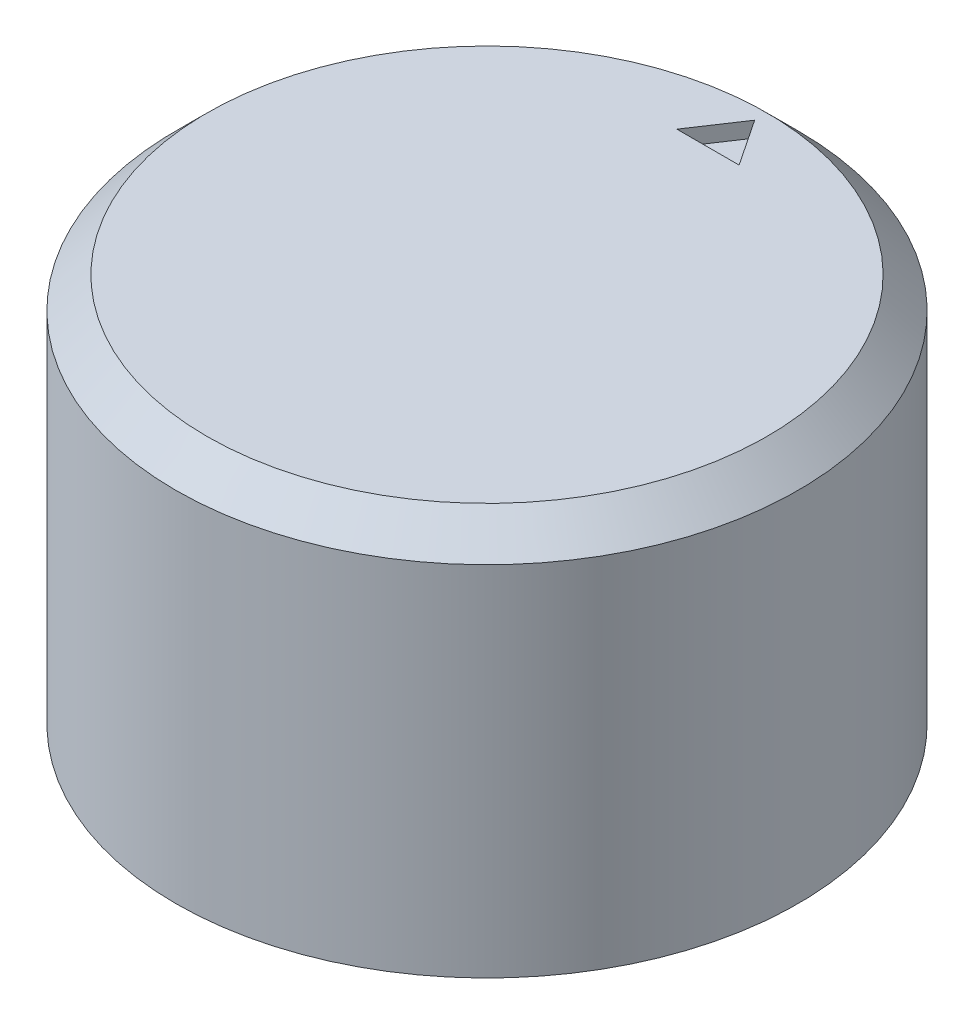
SolidWorks part; units mm, degrees
ref_plane "Front Plane" through (0, 0, 0) normal (0, 0, 1) x (1, 0, 0)
ref_plane "Top Plane" through (0, 0, 0) normal (0, 1, 0) x (1, 0, 0)
ref_plane "Right Plane" through (0, 0, 0) normal (1, 0, 0) x (0, 0, -1)
sketch "Sketch1" plane through (0, 0, 0) normal (0, 1, 0) x (1, 0, 0)
  circle A0 centre (0, 0) radius 10
  dimension "D1" = 20
extrude "Boss-Extrude1" add sketch "Sketch1" along normal blind 12.5
sketch "Sketch2" plane through (0, 0, 0) normal (0, -1, 0) x (1, 0, 0)
  line L0 (-2.5981, 1.5) -> (2.5981, 1.5)
  arc A0 (-2.5981, 1.5) -> (2.5981, 1.5) centre (0, 0) ccw
  dimension "D1" = 6
  dimension "D2" = 1.5
extrude "Cut-Extrude1" cut sketch "Sketch2" against normal blind 10
sketch "Sketch3" plane through (0, 12.5, 0) normal (0, 1, 0) x (1, 0, 0)
  line L0 (-1, 7.1) -> (0, 8.6)
  line L1 (0, 8.6) -> (1, 7.1)
  line L2 (1, 7.1) -> (-1, 7.1)
  point P2 (0, 7.1)
  dimension "D1" = 2
  dimension "D2" = 1.5
  dimension "D3" = 7.1
extrude "Cut-Extrude2" cut sketch "Sketch3" against normal blind 0.5
chamfer "Chamfer1" distance 1 angle 45 1 edges at (0, 12.5, 10)
